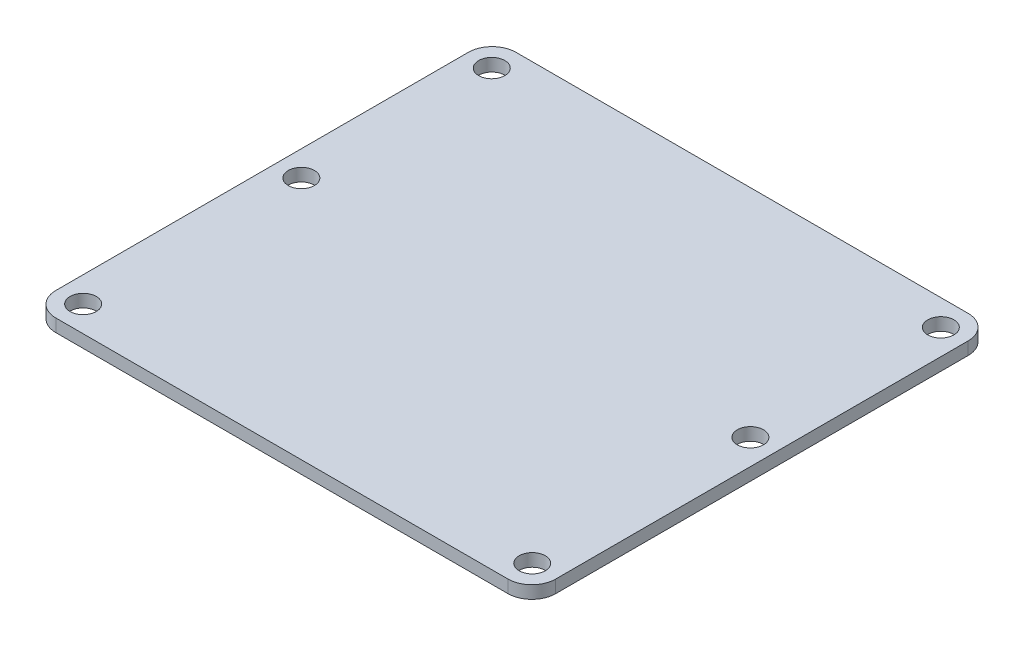
SolidWorks part; units mm, degrees
ref_plane "前视基准面" through (0, 0, 0) normal (0, 0, 1) x (1, 0, 0)
ref_plane "上视基准面" through (0, 0, 0) normal (0, 1, 0) x (1, 0, 0)
ref_plane "右视基准面" through (0, 0, 0) normal (1, 0, 0) x (0, 0, -1)
sketch "草图1" plane through (0, 0, 0) normal (0, 1, 0) x (1, 0, 0)
  line L1 (-31.5, 29) -> (31.5, 29)
  line L2 (-31.5, 29) -> (-31.5, -29)
  line L3 (-31.5, -29) -> (31.5, -29)
  line L4 (31.5, 29) -> (31.5, -29)
  line L5 (-31.5, 29) -> (31.5, -29) construction
  line L6 (-31.5, -29) -> (31.5, 29) construction
  point P0 (0, 0)
  dimension "D1" = 63
  dimension "D2" = 58
extrude "凸台-拉伸1" add sketch "草图1" along normal blind 1.6
sketch "草图2" plane through (0, 1.6, 0) normal (0, 1, 0) x (1, 0, 0)
  line L1 (-28.3, 25.75) -> (28.3, 25.75) construction
  line L2 (-28.3, 25.75) -> (-28.3, -25.75) construction
  line L3 (-28.3, -25.75) -> (28.3, -25.75) construction
  line L4 (28.3, 25.75) -> (28.3, -25.75) construction
  line L5 (-28.3, 25.75) -> (28.3, -25.75) construction
  line L6 (-28.3, -25.75) -> (28.3, 25.75) construction
  circle A0 centre (-28.3, 25.75) radius 1.65
  circle A1 centre (28.3, 25.75) radius 1.65
  circle A2 centre (28.3, -25.75) radius 1.65
  circle A3 centre (-28.3, -25.75) radius 1.65
  point P0 (0, 0)
  dimension "D3" = 3.3
  dimension "D1" = 56.6
  dimension "D2" = 51.5
extrude "切除-拉伸1" cut sketch "草图2" against normal blind 1.6
fillet "圆角1" radius 3 4 edges at (-31.5, 0.8, 29) (-31.5, 0.8, -29) (31.5, 0.8, -29) (31.5, 0.8, 29)
sketch "草图3" plane through (0, 1.6, 0) normal (0, 1, 0) x (1, 0, 0)
  line L0 (0, -0.88) -> (0, 0.88) construction
  circle A0 centre (-28.3, 1.75) radius 1.65
  circle A2 centre (28.3, 1.75) radius 1.65
  circle A3 centre (28.3, -25.75) radius 1.65 construction
  circle A4 centre (-28.3, 25.75) radius 1.65 construction
  point P2 (0, 0)
  point P3 (-28.3, -25.75)
  point P9 (-28.3, -5.9604)
  point P10 (28.3, -11.8931)
  dimension "D1" = 27.5
extrude "切除-拉伸2" cut sketch "草图3" against normal blind 1.6
